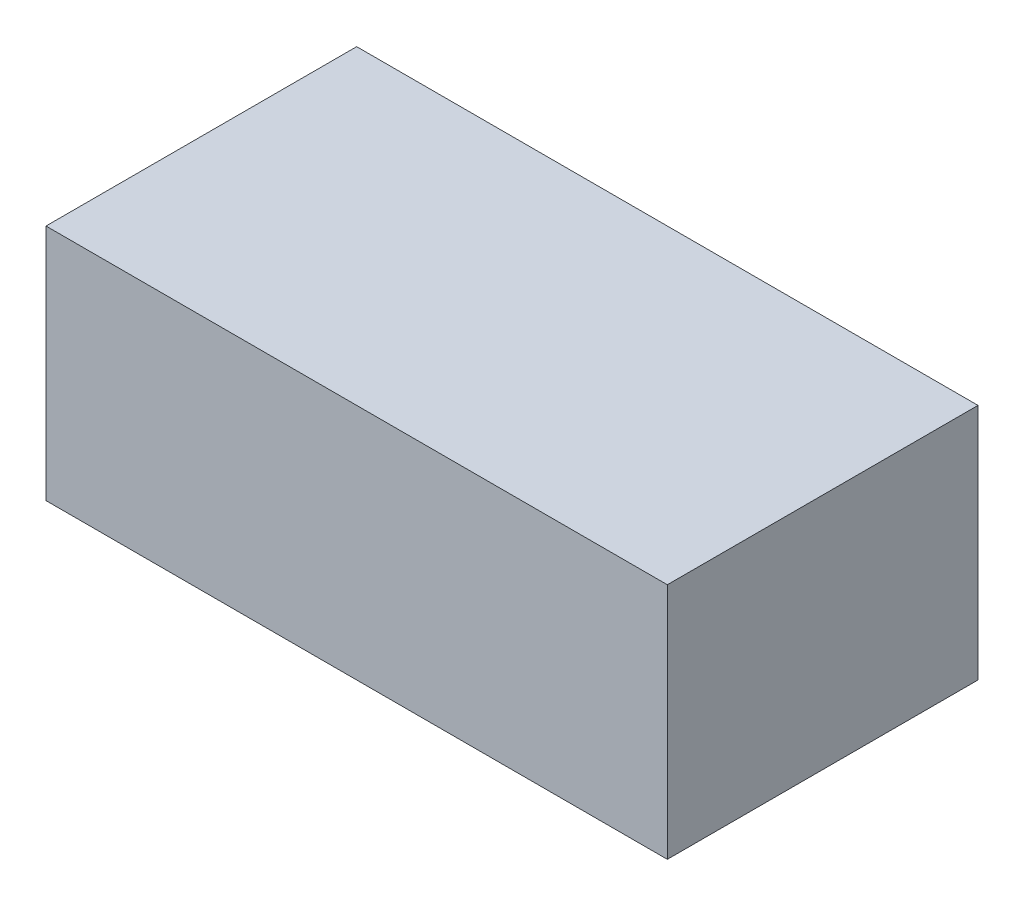
SolidWorks part; units mm, degrees
ref_plane "Front Plane" through (0, 0, 0) normal (0, 0, 1) x (1, 0, 0)
ref_plane "Top Plane" through (0, 0, 0) normal (0, 1, 0) x (1, 0, 0)
ref_plane "Right Plane" through (0, 0, 0) normal (1, 0, 0) x (0, 0, -1)
sketch "Sketch2" plane through (0, 0, 0) normal (0, 1, 0) x (1, 0, 0)
  line L1 (-145, -72.5) -> (145, -72.5)
  line L2 (-145, -72.5) -> (-145, 72.5)
  line L3 (-145, 72.5) -> (145, 72.5)
  line L4 (145, -72.5) -> (145, 72.5)
  line L5 (-145, -72.5) -> (145, 72.5) construction
  line L6 (-145, 72.5) -> (145, -72.5) construction
  point P0 (0, 0)
  dimension "D1" = 145
  dimension "D2" = 290
extrude "Boss-Extrude1" add sketch "Sketch2" along normal blind 111
